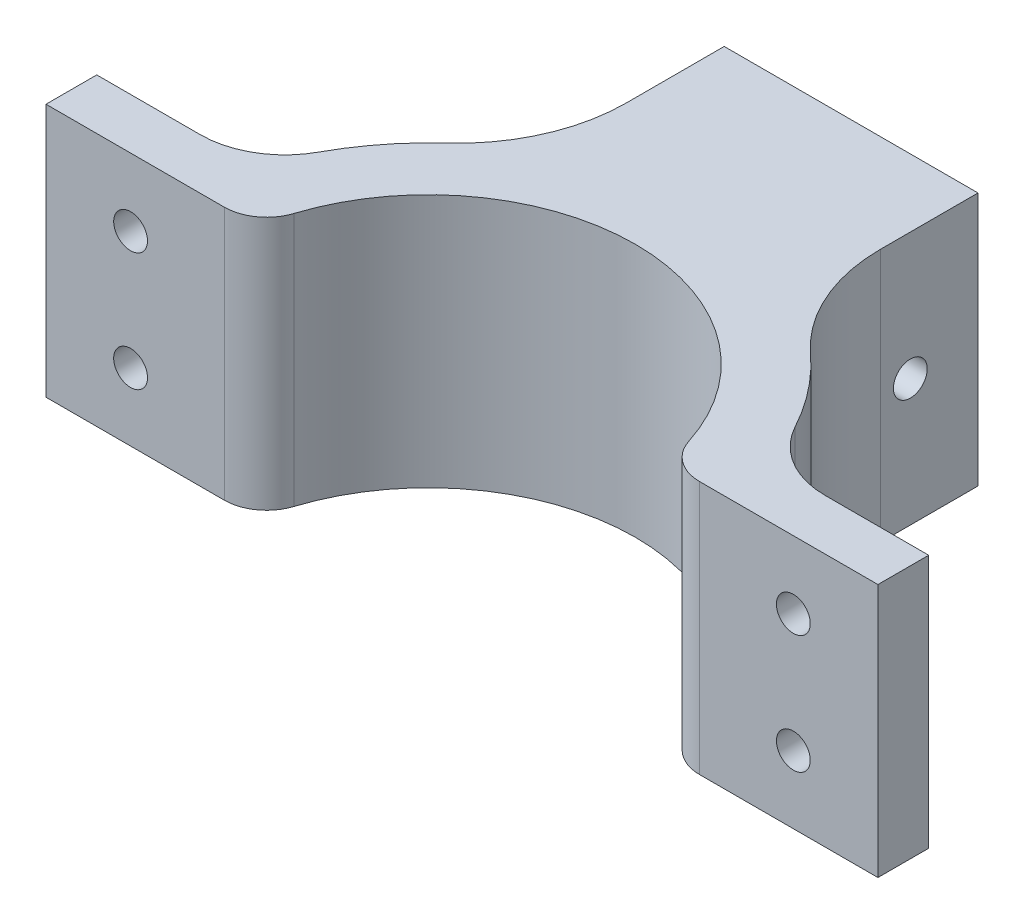
SolidWorks part; units mm, degrees
material "ABS"
ref_plane "Front Plane" through (0, 0, 0) normal (0, 0, 1) x (1, 0, 0)
ref_plane "Top Plane" through (0, 0, 0) normal (0, 1, 0) x (1, 0, 0)
ref_plane "Right Plane" through (0, 0, 0) normal (1, 0, 0) x (0, 0, -1)
sketch "Sketch1" plane through (0, 0, 0) normal (0, 1, 0) x (1, 0, 0)
  line L0 (-22.3663, 10) -> (-30.3974, 10)
  line L1 (-24.1713, 10) -> (-24.1713, 4)
  line L2 (-24.1713, 4) -> (-24.1713, 10)
  line L3 (-24.1713, 4) -> (-49.1713, 4)
  line L4 (-24.1713, 10) -> (-49.1713, 10)
  line L5 (-49.1713, 4) -> (-49.1713, 10)
  line L6 (0, 0) -> (0, 32) construction
  line L7 (24.1713, 10) -> (49.1713, 10)
  line L8 (49.1713, 4) -> (49.1713, 10)
  line L9 (24.1713, 4) -> (49.1713, 4)
  line L10 (24.1713, 10) -> (24.1713, 4)
  line L11 (22.3663, 10) -> (30.3974, 10)
  circle A0 centre (0, 0) radius 24.5
  circle A1 centre (0, 0) radius 32
  dimension "D1" = 49
  dimension "D2" = 64
  dimension "D3" = 10
  dimension "D4" = 6
  dimension "D5" = 25
extrude "Boss-Extrude1" add sketch "Sketch1" along normal blind 30 contours A1 L4 L5 L3 | A0 L0 L1 | L0 A1 L3 L1 | A0 L6 A1 L0 | L6 A0 L11 L7 A1 | A0 L10 L11 | L9 A1 L7 L10 | A1 L9 L8 L7
sketch "Sketch2" plane through (0, 0, -10) normal (0, 0, -1) x (-1, 0, 0)
  line L0 (-30.3974, 30) -> (-49.1713, 30) construction
  line L1 (-30.3974, 0) -> (-49.1713, 0) construction
  line L2 (-49.1713, 30) -> (-49.1713, 0) construction
  line L3 (0, 0) -> (0, 30) construction
  line L4 (30.3974, 30) -> (-30.3974, 30) construction
  circle A0 centre (-39.1713, 22) radius 2
  circle A1 centre (-39.1713, 8) radius 2
  circle A2 centre (39.1713, 8) radius 2
  circle A3 centre (39.1713, 22) radius 2
  dimension "D1" = 4
  dimension "D2" = 4
  dimension "D3" = 8
  dimension "D4" = 8
  dimension "D5" = 10
  dimension "D6" = 10
extrude "Cut-Extrude1" cut sketch "Sketch2" against normal through all
fillet "Fillet1" radius 10 2 edges at (30.3974, 15, -10) (-30.3974, 15, -10)
fillet "Fillet2" radius 5 2 edges at (-24.1713, 15, -4) (24.1713, 15, -4)
sketch "Sketch3" plane through (0, 0, -10) normal (0, 0, -1) x (-1, 0, 0)
  line L0 (0, 30) -> (0, 0) construction
  line L1 (28.1389, 30) -> (-28.1389, 30) construction
  line L2 (-28.1389, 0) -> (28.1389, 0) construction
  line L3 (-28.1389, 15) -> (28.1389, 15) construction
  line L4 (-28.1389, 30) -> (-28.1389, 0) construction
  line L5 (28.1389, 0) -> (28.1389, 30) construction
  line L7 (-15, 0) -> (15, 0)
  line L8 (-15, 0) -> (-15, 30)
  line L9 (-15, 30) -> (15, 30)
  line L10 (15, 0) -> (15, 30)
  line L11 (-15, 0) -> (15, 30) construction
  line L12 (-15, 30) -> (15, 0) construction
  line L13 (-9.25, 5.75) -> (9.25, 5.75)
  line L14 (-9.25, 5.75) -> (-9.25, 24.25)
  line L15 (-9.25, 24.25) -> (9.25, 24.25)
  line L16 (9.25, 5.75) -> (9.25, 24.25)
  line L17 (-9.25, 5.75) -> (9.25, 24.25) construction
  line L18 (-9.25, 24.25) -> (9.25, 5.75) construction
  point P12 (0, 15)
  point P17 (0, 15)
  dimension "D1" = 30
  dimension "D2" = 30
  dimension "D3" = 18.5
extrude "Boss-Extrude2" add sketch "Sketch3" along normal blind 25 from offset 15
fillet "Fillet3" radius 20 2 edges at (15, 15, -28.2666) (-15, 15, -28.2666)
sketch "Sketch4" plane through (15, 0, 0) normal (1, 0, 0) x (0, 0, -1)
  line L0 (50, 30) -> (38.4578, 30) construction
  line L1 (50, 30) -> (50, 0) construction
  circle A0 centre (42, 15) radius 2
  dimension "D1" = 4
  dimension "D2" = 15
  dimension "D3" = 8
extrude "Cut-Extrude2" cut sketch "Sketch4" against normal up to surface (30 mm away) up to face at (-15, 15, -44.2289)
